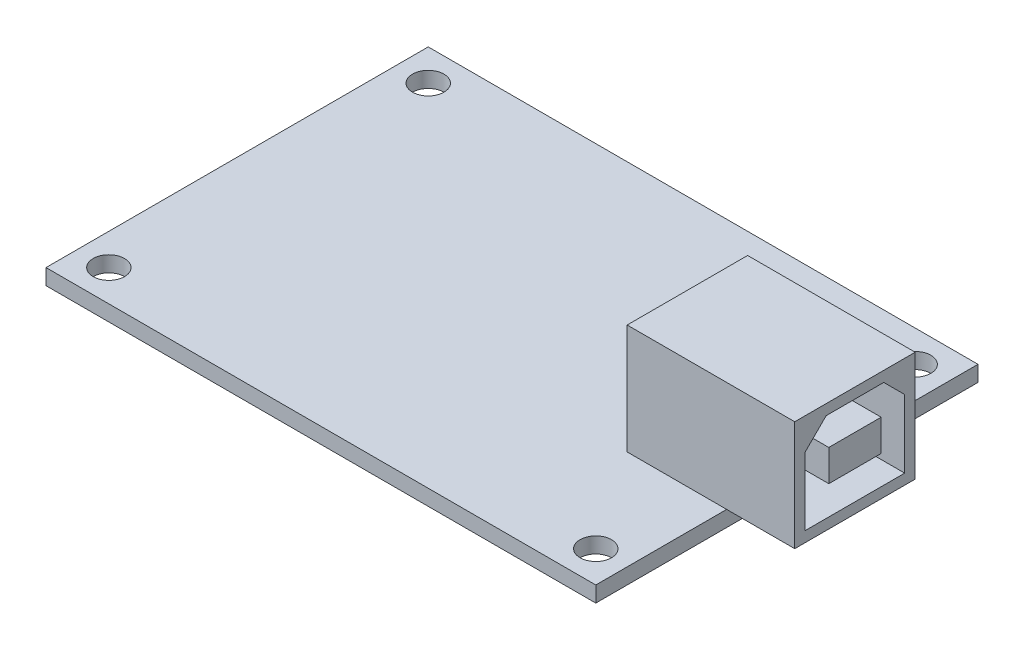
SolidWorks part; units mm, degrees
ref_plane "Front Plane" through (0, 0, 0) normal (0, 0, 1) x (1, 0, 0)
ref_plane "Top Plane" through (0, 0, 0) normal (0, 1, 0) x (1, 0, 0)
ref_plane "Right Plane" through (0, 0, 0) normal (1, 0, 0) x (0, 0, -1)
sketch "Sketch1" plane through (0, 0, 0) normal (0, 1, 0) x (1, 0, 0)
  line L1 (-26.25, 18.25) -> (26.25, 18.25)
  line L2 (-26.25, 18.25) -> (-26.25, -18.25)
  line L3 (-26.25, -18.25) -> (26.25, -18.25)
  line L4 (26.25, 18.25) -> (26.25, -18.25)
  line L5 (-26.25, 18.25) -> (26.25, -18.25) construction
  line L6 (-26.25, -18.25) -> (26.25, 18.25) construction
  circle A0 centre (-23.25, 15.25) radius 1.5
  circle A1 centre (23.25, 15.25) radius 1.5
  circle A2 centre (-23.25, -15.25) radius 1.5
  circle A3 centre (23.25, -15.25) radius 1.5
  point P0 (0, 0)
  point P14 (0, 0)
  point P15 (0, 0)
  point P16 (26.25, 13.9706)
  point P18 (24.1839, -14.4873)
  dimension "D3" = 3
  dimension "D1" = 52.5
  dimension "D2" = 36.5
  dimension "D4" = 3
  dimension "D5" = 3
  dimension "D6" = 3
  dimension "D7" = 3
  dimension "D8" = 3
  dimension "D9" = 3
  dimension "D10" = 3
  dimension "D11" = 3
extrude "Boss-Extrude1" add sketch "Sketch1" along normal blind 1.5 contours L3 L4 L1 L2
sketch "Sketch2" plane through (0, 1.5, 0) normal (0, 1, 0) x (1, 0, 0)
  line L1 (16.75, 5.75) -> (32.75, 5.75)
  line L2 (16.75, 5.75) -> (16.75, -5.75)
  line L3 (16.75, -5.75) -> (32.75, -5.75)
  line L4 (32.75, 5.75) -> (32.75, -5.75)
  line L5 (16.75, 5.75) -> (32.75, -5.75) construction
  line L6 (16.75, -5.75) -> (32.75, 5.75) construction
  line L7 (26.25, -18.25) -> (26.25, 18.25) construction
  point P0 (24.75, 0)
  point P5 (24.5646, 0)
  point P7 (0, 0)
  point P9 (0, 0)
  dimension "D1" = 16
  dimension "D2" = 11.5
  dimension "D3" = 6.5
extrude "Boss-Extrude2" add sketch "Sketch2" along normal blind 10.5
sketch "Sketch7" plane through (32.75, 0, 0) normal (1, 0, 0) x (0, 0, -1)
  line L0 (-4.75, 2.5) -> (4.75, 2.5)
  line L1 (4.75, 2.5) -> (4.75, 9)
  line L2 (4.75, 9) -> (2.75, 11)
  line L3 (2.75, 11) -> (-2.75, 11)
  line L4 (-2.75, 11) -> (-4.75, 9)
  line L5 (-4.75, 9) -> (-4.75, 2.5)
  line L6 (-5.75, 12) -> (5.75, 12) construction
  line L7 (-2.5, 8.25) -> (2.5, 8.25)
  line L8 (-2.5, 8.25) -> (-2.5, 5.25)
  line L9 (-2.5, 5.25) -> (2.5, 5.25)
  line L10 (2.5, 8.25) -> (2.5, 5.25)
  line L11 (-2.5, 8.25) -> (2.5, 5.25) construction
  line L12 (-2.5, 5.25) -> (2.5, 8.25) construction
  line L13 (-5.75, 12) -> (-5.75, 1.5) construction
  line L14 (5.75, 12) -> (5.75, 1.5) construction
  line L15 (-5.75, 1.5) -> (5.75, 1.5) construction
  point P5 (0, 6.75)
  point P19 (0, 0)
  point P21 (0, 0)
  point P22 (0, 0)
  point P23 (-5.75, 6.75)
  point P24 (0, 0)
  dimension "D1" = 1
  dimension "D2" = 1
  dimension "D3" = 1
  dimension "D4" = 1
  dimension "D5" = 5
  dimension "D6" = 3
  dimension "D7" = 2
  dimension "D8" = 2
  dimension "D9" = 2
extrude "Cut-Extrude1" cut sketch "Sketch7" against normal blind 10
